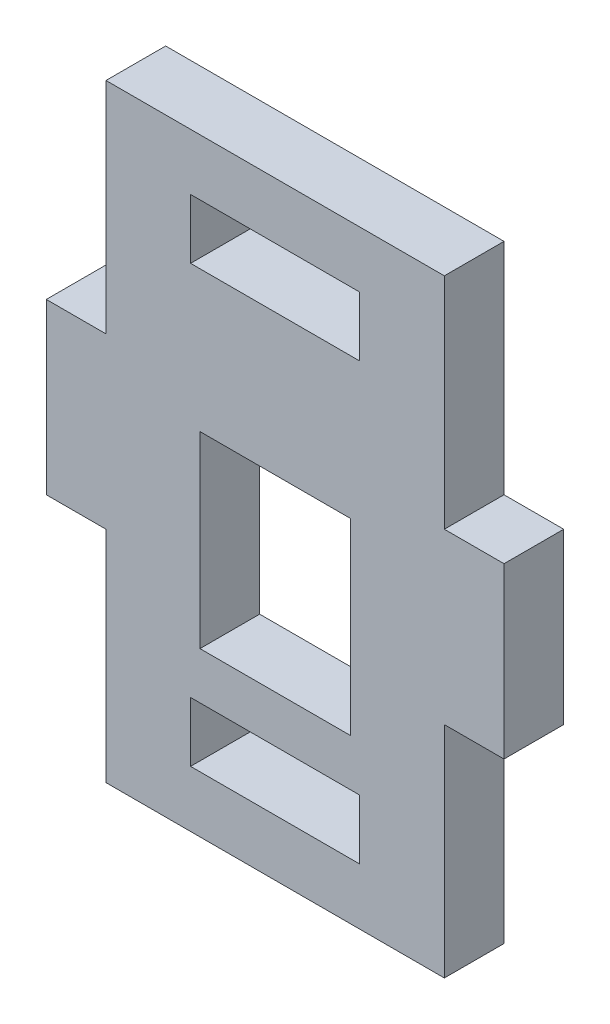
SolidWorks part; units mm, degrees
ref_plane "Front Plane" through (0, 0, 0) normal (0, 0, 1) x (1, 0, 0)
ref_plane "Top Plane" through (0, 0, 0) normal (0, 1, 0) x (1, 0, 0)
ref_plane "Right Plane" through (0, 0, 0) normal (1, 0, 0) x (0, 0, -1)
sketch "Sketch2" plane through (0, 0, 0) normal (0, 0, 1) x (1, 0, 0)
  line L0 (0, 0) -> (18, 0)
  line L1 (18, 0) -> (18, 11.675)
  line L2 (18, 11.675) -> (21.175, 11.675)
  line L3 (21.175, 11.675) -> (21.175, 20.675)
  line L4 (21.175, 20.675) -> (18, 20.675)
  line L5 (18, 20.675) -> (18, 32.35)
  line L6 (18, 32.35) -> (0, 32.35)
  line L7 (0, 32.35) -> (0, 20.675)
  line L8 (0, 20.675) -> (-3.175, 20.675)
  line L9 (-3.175, 20.675) -> (-3.175, 11.675)
  line L10 (-3.175, 11.675) -> (0, 11.675)
  line L11 (0, 11.675) -> (0, 0)
  line L12 (9, 50.5519) -> (9, -2.1862) construction
  line L13 (-3.175, 16.175) -> (57.251, 16.175) construction
  line L14 (9, 29.35) -> (4.5, 29.35)
  line L15 (4.5, 29.35) -> (4.5, 26.175)
  line L16 (4.5, 26.175) -> (13.5, 26.175)
  line L17 (9, 32.35) -> (9, 29.35) construction
  line L18 (13.5, 26.175) -> (13.5, 29.35)
  line L19 (13.5, 29.35) -> (9, 29.35)
  line L20 (13.5, 3) -> (9, 3)
  line L21 (13.5, 6.175) -> (13.5, 3)
  line L22 (4.5, 6.175) -> (13.5, 6.175)
  line L23 (4.5, 3) -> (4.5, 6.175)
  line L24 (9, 3) -> (4.5, 3)
  line L25 (9, 0) -> (9, 3) construction
  line L29 (13.5, 26.175) -> (18, 26.175)
  line L33 (9, 8.675) -> (13, 8.675)
  line L34 (13, 8.675) -> (13, 18.675)
  line L35 (13, 18.675) -> (5, 18.675)
  line L36 (5, 18.675) -> (5, 8.675)
  line L37 (5, 8.675) -> (9, 8.675)
  dimension "D1" = 3.175
  dimension "D2" = 9
  dimension "D3" = 18
  dimension "D4" = 20
  dimension "D5" = 3
  dimension "D6" = 8
  dimension "D7" = 10
  dimension "D8" = 2.5
extrude "Boss-Extrude1" add sketch "Sketch2" along normal mid plane 3.175
